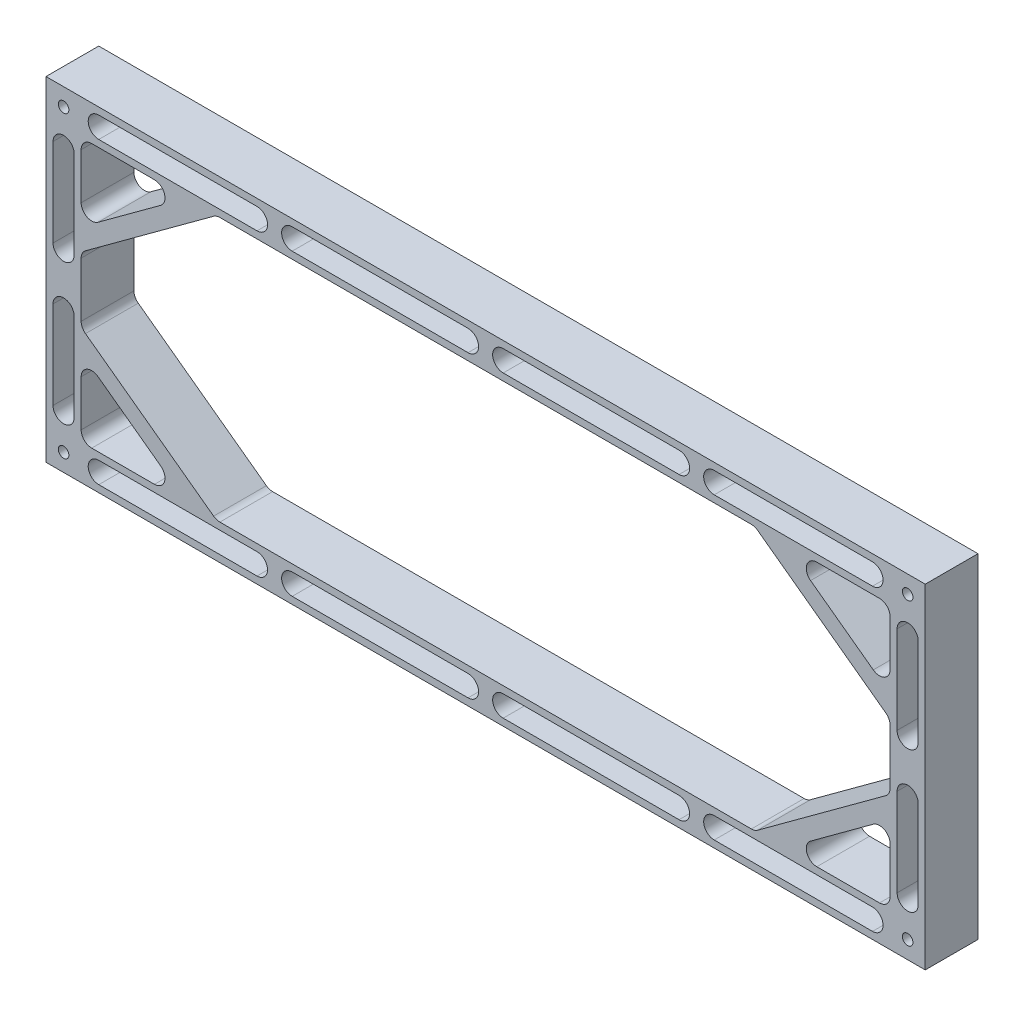
SolidWorks part; units mm, degrees
material "2014 Alloy"
ref_plane "Front Plane" through (0, 0, 0) normal (0, 0, 1) x (1, 0, 0)
ref_plane "Top Plane" through (0, 0, 0) normal (0, 1, 0) x (1, 0, 0)
ref_plane "Right Plane" through (0, 0, 0) normal (1, 0, 0) x (0, 0, -1)
sketch "Sketch1" plane through (0, 0, 0) normal (0, 0, 1) x (1, 0, 0)
  line L0 (0, 0) -> (250, 0)
  line L1 (250, 0) -> (250, 95)
  line L2 (250, 95) -> (0, 95)
  line L3 (0, 95) -> (0, 0)
  line L4 (10, 85) -> (10, 10)
  line L5 (10, 10) -> (240, 10)
  line L6 (240, 10) -> (240, 85)
  line L7 (240, 85) -> (10, 85)
  line L8 (10, 63) -> (40, 85)
  line L9 (0, 47.5) -> (250, 47.5) construction
  line L10 (125, 95) -> (125, 0) construction
  line L11 (10, 56.7996) -> (48.455, 85)
  line L12 (10, 32) -> (40, 10)
  line L13 (10, 38.2004) -> (48.455, 10)
  line L14 (240, 63) -> (210, 85)
  line L15 (240, 56.7996) -> (201.545, 85)
  line L16 (240, 32) -> (210, 10)
  line L17 (240, 38.2004) -> (201.545, 10)
  dimension "D1" = 95
  dimension "D2" = 250
  dimension "D3" = 10
  dimension "D4" = 10
  dimension "D5" = 10
  dimension "D6" = 10
  dimension "D7" = 30
  dimension "D8" = 22
  dimension "D9" = 5
extrude "Boss-Extrude1" add sketch "Sketch1" along normal blind 15 contours L2 L3 L0 L1 L7 L6 L5 L4 | L4 L11 L7 L8 | L13 L4 L12 L5 | L6 L17 L5 L16 | L15 L6 L14 L7
fillet "Fillet1" radius 3 20 edges at (210, 85, 7.5) (240, 63, 7.5) (240, 85, 7.5) (201.545, 85, 7.5) (240, 32, 7.5) (210, 10, 7.5) (240, 56.7996, 7.5) (240, 38.2004, 7.5) (201.545, 10, 7.5) (240, 10, 7.5) (40, 10, 7.5) (10, 32, 7.5) (10, 10, 7.5) (48.455, 10, 7.5) (10, 38.2004, 7.5) (10, 56.7996, 7.5) (48.455, 85, 7.5) (40, 85, 7.5) (10, 63, 7.5) (10, 85, 7.5)
sketch "Sketch11" plane through (0, 0, 0) normal (0, 0, -1) x (-1, 0, 0)
  line L0 (-5, 80) -> (-5, 55) construction
  line L1 (-5, 40) -> (-5, 15) construction
  line L2 (-15, 90) -> (-60, 90) construction
  line L3 (-70, 90) -> (-120, 90) construction
  line L4 (-130, 90) -> (-180, 90) construction
  line L5 (-190, 90) -> (-235, 90) construction
  line L6 (0, 95) -> (0, 0) construction
  line L7 (-250, 95) -> (0, 95) construction
  line L8 (-250, 0) -> (-250, 95) construction
  line L10 (0, 0) -> (-250, 0) construction
  line L11 (-250, 47.5) -> (0, 47.5) construction
  line L12 (-125, 95) -> (-125, 0) construction
  line L13 (-15, 5) -> (-60, 5) construction
  line L14 (-70, 5) -> (-120, 5) construction
  line L15 (-130, 5) -> (-180, 5) construction
  line L16 (-190, 5) -> (-235, 5) construction
  line L17 (-245, 40) -> (-245, 15) construction
  line L18 (-245, 80) -> (-245, 55) construction
  line L19 (-248, 80) -> (-248, 55)
  line L20 (-248, 40) -> (-248, 15)
  line L21 (-190, 8) -> (-235, 8)
  line L22 (-130, 8) -> (-180, 8)
  line L23 (-70, 8) -> (-120, 8)
  line L24 (-15, 8) -> (-60, 8)
  line L25 (-8, 40) -> (-8, 15)
  line L26 (-8, 80) -> (-8, 55)
  line L27 (-15, 93) -> (-60, 93)
  line L28 (-70, 93) -> (-120, 93)
  line L29 (-130, 93) -> (-180, 93)
  line L30 (-190, 93) -> (-235, 93)
  line L31 (-242, 80) -> (-242, 55)
  line L32 (-242, 40) -> (-242, 15)
  line L33 (-190, 2) -> (-235, 2)
  line L34 (-130, 2) -> (-180, 2)
  line L35 (-70, 2) -> (-120, 2)
  line L36 (-15, 2) -> (-60, 2)
  line L37 (-2, 40) -> (-2, 15)
  line L38 (-2, 80) -> (-2, 55)
  line L39 (-15, 87) -> (-60, 87)
  line L40 (-70, 87) -> (-120, 87)
  line L41 (-130, 87) -> (-180, 87)
  line L42 (-190, 87) -> (-235, 87)
  arc A0 (-248, 80) -> (-242, 80) centre (-245, 80) cw
  arc A1 (-248, 55) -> (-242, 55) centre (-245, 55) ccw
  arc A2 (-248, 40) -> (-242, 40) centre (-245, 40) cw
  arc A3 (-248, 15) -> (-242, 15) centre (-245, 15) ccw
  arc A4 (-190, 8) -> (-190, 2) centre (-190, 5) cw
  arc A5 (-235, 8) -> (-235, 2) centre (-235, 5) ccw
  arc A6 (-130, 8) -> (-130, 2) centre (-130, 5) cw
  arc A7 (-180, 8) -> (-180, 2) centre (-180, 5) ccw
  arc A8 (-70, 8) -> (-70, 2) centre (-70, 5) cw
  arc A9 (-120, 8) -> (-120, 2) centre (-120, 5) ccw
  arc A10 (-15, 8) -> (-15, 2) centre (-15, 5) cw
  arc A11 (-60, 8) -> (-60, 2) centre (-60, 5) ccw
  arc A12 (-8, 40) -> (-2, 40) centre (-5, 40) cw
  arc A13 (-8, 15) -> (-2, 15) centre (-5, 15) ccw
  arc A14 (-8, 80) -> (-2, 80) centre (-5, 80) cw
  arc A15 (-8, 55) -> (-2, 55) centre (-5, 55) ccw
  arc A16 (-15, 93) -> (-15, 87) centre (-15, 90) cw
  arc A17 (-60, 93) -> (-60, 87) centre (-60, 90) ccw
  arc A18 (-70, 93) -> (-70, 87) centre (-70, 90) cw
  arc A19 (-120, 93) -> (-120, 87) centre (-120, 90) ccw
  arc A20 (-130, 93) -> (-130, 87) centre (-130, 90) cw
  arc A21 (-180, 93) -> (-180, 87) centre (-180, 90) ccw
  arc A22 (-190, 93) -> (-190, 87) centre (-190, 90) cw
  arc A23 (-235, 93) -> (-235, 87) centre (-235, 90) ccw
  dimension "D1" = 5
  dimension "D2" = 15
  dimension "D3" = 15
  dimension "D4" = 25
  dimension "D5" = 15
  dimension "D6" = 5
  dimension "D7" = 15
  dimension "D8" = 10
  dimension "D9" = 10
  dimension "D10" = 10
  dimension "D11" = 45
  dimension "D12" = 45
  dimension "D13" = 15
  dimension "D14" = 50
  dimension "D15" = 3
  dimension "D16" = 3
extrude "Cut-Extrude2" cut sketch "Sketch11" against normal through all
hole_wizard "CBORE for M1.6 Hex Head Cap Screw1" positions "Sketch13" profile "Sketch12" counterbore size "M1.6" standard "ISO" end condition through all
sketch "Sketch13" plane through (0, 0, 0) normal (0, 0, -1) x (-1, 0, 0)
  line L0 (-250, 0) -> (-250, 95) construction
  line L1 (-250, 95) -> (0, 95) construction
  line L2 (0, 0) -> (-250, 0) construction
  line L3 (0, 95) -> (0, 0) construction
  point P0 (-245, 90)
  point P2 (-245, 5)
  point P4 (-5, 5)
  point P6 (-5, 90)
  dimension "D1" = 5
  dimension "D2" = 5
  dimension "D3" = 5
  dimension "D4" = 5
sketch "Sketch12" plane through (245, 90, 0) normal (1, 0, 0) x (0, 1, 0)
  line L0 (0, 0) -> (0, 15)
  line L1 (0, 15) -> (1.5, 15)
  line L3 (1.5, 15) -> (1.5, 5)
  line L4 (1.5, 5) -> (2.5, 5)
  line L5 (2.5, 5) -> (2.5, 0)
  line L7 (2.5, 0) -> (0, 0)
  line L11 (0, -6.35) -> (0, 107.95) construction
  dimension "Thru Hole Dia." = 3
  dimension "Thru Hole Depth" = 15
  dimension "C'Bore Dia." = 5
  dimension "C'Bore Depth" = 5
